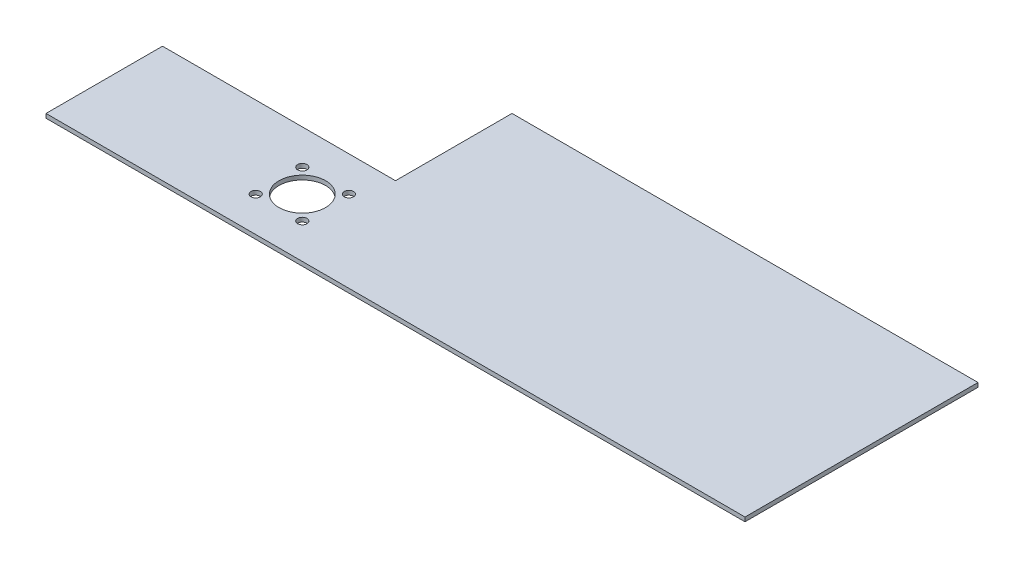
SolidWorks part; units mm, degrees
ref_plane "前视基准面" through (0, 0, 0) normal (0, 0, 1) x (1, 0, 0)
ref_plane "上视基准面" through (0, 0, 0) normal (0, 1, 0) x (1, 0, 0)
ref_plane "右视基准面" through (0, 0, 0) normal (1, 0, 0) x (0, 0, -1)
sketch "草图1" plane through (0, 0, 0) normal (0, 1, 0) x (1, 0, 0)
  line L1 (0, 0) -> (300, 0)
  line L2 (0, 0) -> (0, 100)
  line L3 (0, 100) -> (300, 100)
  line L4 (300, 0) -> (300, 100)
  dimension "D1" = 100
  dimension "D2" = 300
extrude "凸台-拉伸1" add sketch "草图1" along normal blind 1.8
sketch "草图2" plane through (0, 1.8, 0) normal (0, 1, 0) x (1, 0, 0)
  line L1 (100, 50) -> (0, 50)
  line L2 (100, 50) -> (100, 100)
  line L3 (100, 100) -> (0, 100)
  line L4 (0, 50) -> (0, 100)
  dimension "D1" = 50
  dimension "D2" = 100
extrude "切除-拉伸1" cut sketch "草图2" against normal through all
sketch "草图3" plane through (0, 1.8, 0) normal (0, 1, 0) x (1, 0, 0)
  line L0 (0, 50) -> (100, 50) construction
  line L1 (100, 50) -> (100, 100) construction
  circle A0 centre (95, 35) radius 2
  circle A1 centre (75, 35) radius 2
  circle A2 centre (75, 15) radius 2
  circle A3 centre (95, 15) radius 2
  circle A4 centre (85, 25) radius 10
  point P12 (96.9815, 24.3829)
  dimension "D1" = 4
  dimension "D2" = 4
  dimension "D3" = 4
  dimension "D4" = 4
  dimension "D5" = 20
  dimension "D6" = 20
  dimension "D7" = 20
  dimension "D8" = 20
  dimension "D9" = 20
  dimension "D10" = 10
  dimension "D11" = 10
  dimension "D12" = 25
  dimension "D13" = 15
extrude "切除-拉伸2" cut sketch "草图3" against normal through all
